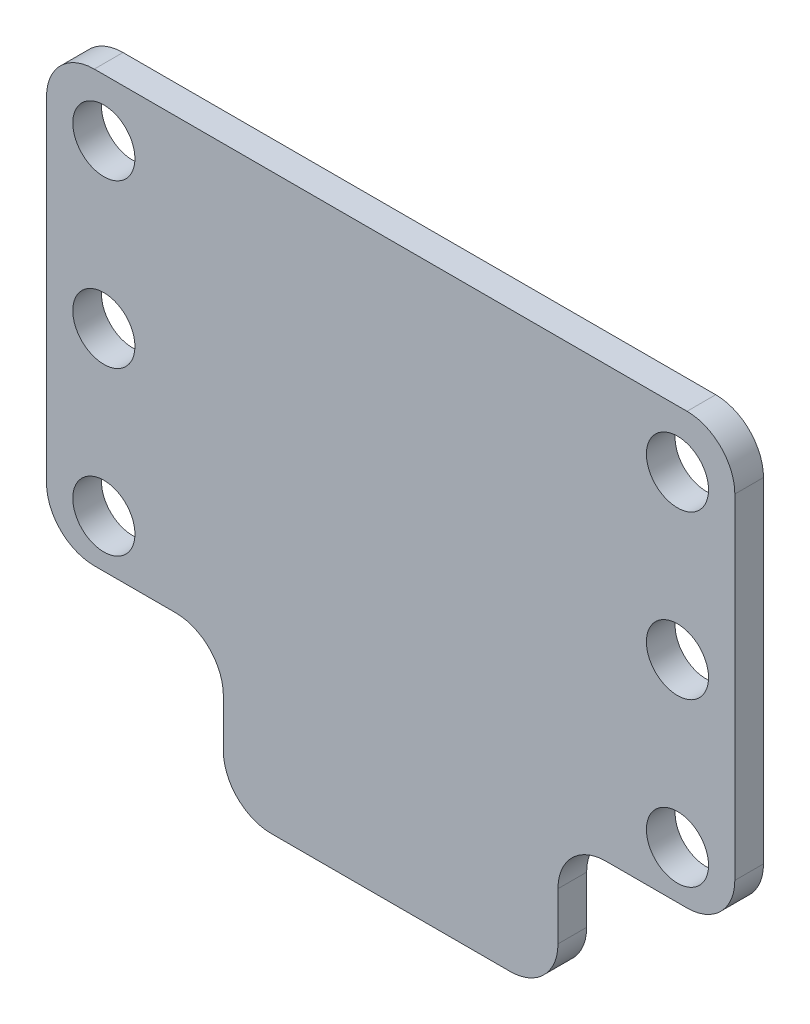
SolidWorks part; units mm, degrees
ref_plane "Plan de face" through (0, 0, 0) normal (0, 0, 1) x (1, 0, 0)
ref_plane "Plan de dessus" through (0, 0, 0) normal (0, 1, 0) x (1, 0, 0)
ref_plane "Plan de droite" through (0, 0, 0) normal (1, 0, 0) x (0, 0, -1)
sketch "Esquisse2" plane through (0, 0, 0) normal (0, 0, 1) x (1, 0, 0)
  line L0 (37.2085, -84.0985) -> (37.2085, -5.0985) construction
  line L1 (109.2085, 1.9015) -> (37.2085, 1.9015)
  line L2 (109.2085, 1.9015) -> (109.2085, -43.0985)
  line L3 (109.2085, -43.0985) -> (90.7085, -43.0985)
  line L4 (37.2085, 1.9015) -> (37.2085, -43.0985)
  line L5 (55.7085, -43.0985) -> (37.2085, -43.0985)
  line L7 (90.7085, -43.0985) -> (90.7085, -58.0985)
  line L8 (90.7085, -58.0985) -> (55.7085, -58.0985)
  line L9 (55.7085, -43.0985) -> (55.7085, -58.0985)
  circle A0 centre (103.2085, -4.0985) radius 3.25
  circle A1 centre (103.2085, -38.0985) radius 3.25
  circle A2 centre (43.2085, -38.0985) radius 3.25
  circle A3 centre (43.2085, -4.0985) radius 3.25
  circle A4 centre (43.2085, -21.0985) radius 3.25
  circle A5 centre (103.2085, -21.0985) radius 3.25
  point P23 (73.2085, -58.0985)
  point P24 (73.2085, 1.9015)
  dimension "D4" = 6.5
  dimension "D1" = 45
  dimension "D2" = 15
  dimension "D3" = 35
  dimension "D5" = 17
extrude "Boss.-Extru.1" add sketch "Esquisse2" along normal blind 3
fillet "Congé1" radius 5 8 edges at (37.2085, 1.9015, 1.5) (37.2085, -43.0985, 1.5) (55.7085, -58.0985, 1.5) (55.7085, -43.0985, 1.5) (90.7085, -58.0985, 1.5) (90.7085, -43.0985, 1.5) (109.2085, -43.0985, 1.5) (109.2085, 1.9015, 1.5)
